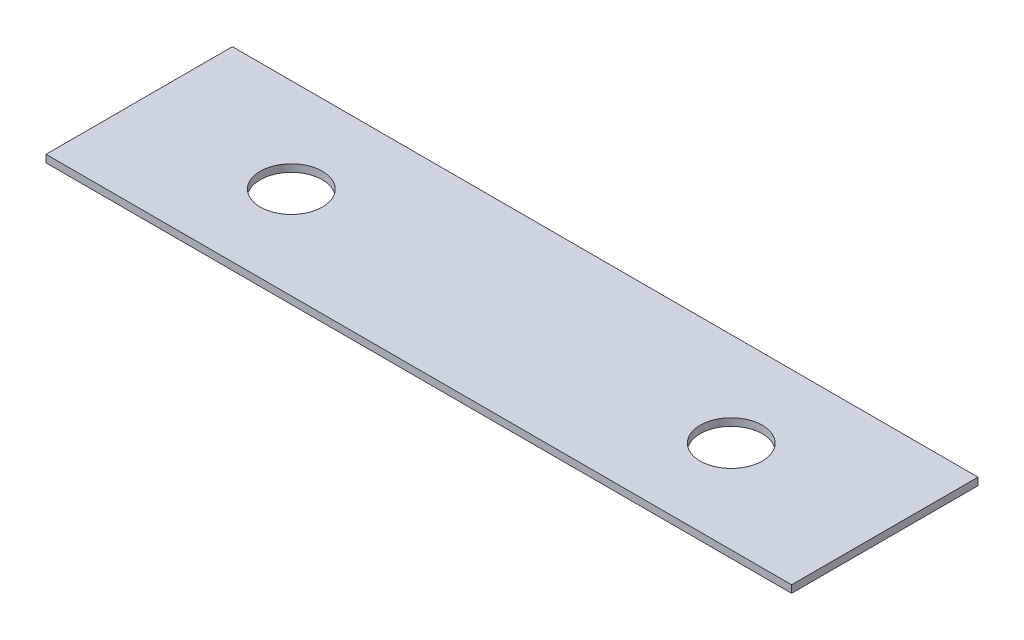
SolidWorks part; units mm, degrees
material "Plain Carbon Steel"
ref_plane "Front Plane" through (0, 0, 0) normal (0, 0, 1) x (1, 0, 0)
ref_plane "Top Plane" through (0, 0, 0) normal (0, 1, 0) x (1, 0, 0)
ref_plane "Right Plane" through (0, 0, 0) normal (1, 0, 0) x (0, 0, -1)
sketch "Sketch1" plane through (0, 0, 0) normal (1, 0, 0) x (0, 0, -1)
  line L1 (0, 0) -> (38.1, 0)
  line L2 (0, 0) -> (0, 1.5189)
  line L3 (0, 1.5189) -> (38.1, 1.5189)
  line L4 (38.1, 0) -> (38.1, 1.5189)
  dimension "D1" = 1.5189
  dimension "D2" = 38.1
extrude "Boss-Extrude1" add sketch "Sketch1" along normal blind 152.4
sketch "Sketch2" plane through (0, 1.5189, 0) normal (0, 1, 0) x (1, 0, 0)
  line L0 (0, 18.9) -> (31.242, 18.9) construction
  line L2 (152.4, 18.9) -> (121.158, 18.9) construction
  line L5 (152.4, 0) -> (0, 0) construction
  line L6 (0, 38.1) -> (0, 0) construction
  line L7 (152.4, 38.1) -> (152.4, 0) construction
  circle A0 centre (31.242, 18.9) radius 6.35
  circle A1 centre (121.158, 18.9) radius 6.35
  dimension "D2" = 12.7
  dimension "D4" = 12.7
  dimension "D1" = 31.242
  dimension "D3" = 31.242
  dimension "D5" = 18.9
extrude "Cut-Extrude1" cut sketch "Sketch2" against normal up to next
